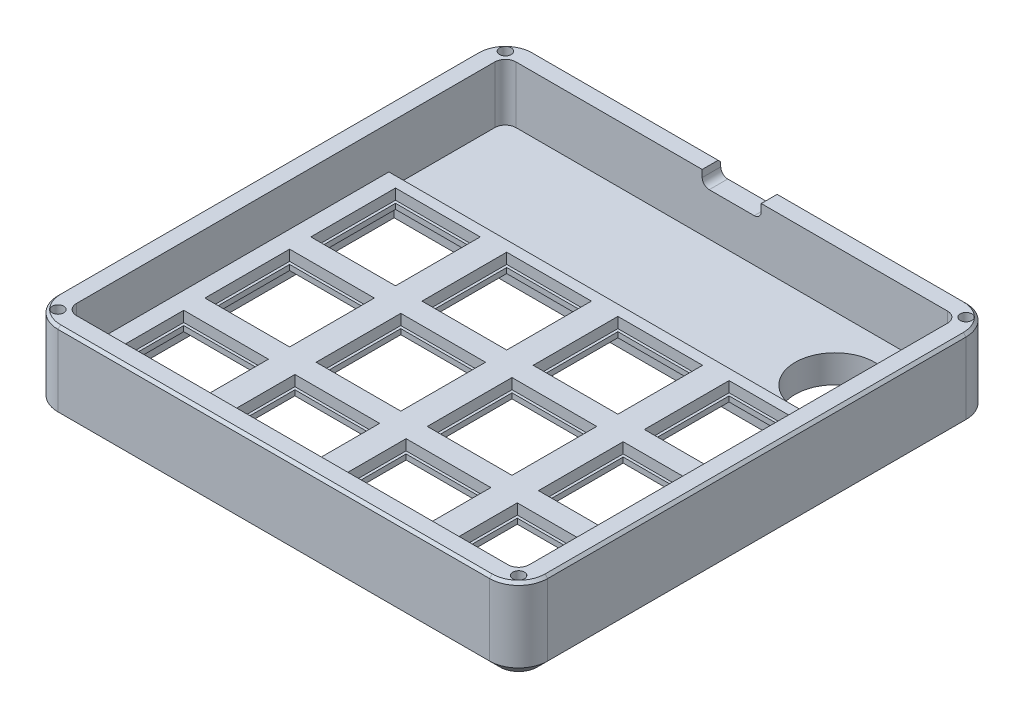
SolidWorks part; units mm, degrees
ref_plane "Front Plane" through (0, 0, 0) normal (0, 0, 1) x (1, 0, 0)
ref_plane "Top Plane" through (0, 0, 0) normal (0, 1, 0) x (1, 0, 0)
ref_plane "Right Plane" through (0, 0, 0) normal (1, 0, 0) x (0, 0, -1)
sketch "Sketch1" plane through (0, 0, 0) normal (0, 1, 0) x (1, 0, 0)
  line L0 (-42.7507, 39.5) -> (-42.7507, -39.5)
  line L1 (-40.75, -41.5007) -> (40.75, -41.5007)
  line L2 (42.7507, -39.5) -> (42.7507, 39.5)
  line L3 (40.75, 41.5007) -> (-40.75, 41.5007)
  line L4 (-42.7507, 0) -> (42.7507, 0) construction
  line L5 (0, 41.5007) -> (0, -41.5007) construction
  line L6 (-46.2507, 39.5) -> (-46.2507, -39.5)
  line L7 (-40.75, -45.0007) -> (40.75, -45.0007)
  line L8 (46.2507, -39.5) -> (46.2507, 39.5)
  line L9 (40.75, 45.0007) -> (-40.75, 45.0007)
  arc A0 (-40.75, 41.5007) -> (-42.7507, 39.5) centre (-40.75, 39.5) ccw
  arc A1 (-42.7507, -39.5) -> (-40.75, -41.5007) centre (-40.75, -39.5) ccw
  arc A2 (40.75, -41.5007) -> (42.7507, -39.5) centre (40.75, -39.5) ccw
  arc A3 (42.7507, 39.5) -> (40.75, 41.5007) centre (40.75, 39.5) ccw
  arc A4 (-40.75, 45.0007) -> (-46.2507, 39.5) centre (-40.75, 39.5) ccw
  arc A5 (-46.2507, -39.5) -> (-40.75, -45.0007) centre (-40.75, -39.5) ccw
  arc A6 (40.75, -45.0007) -> (46.2507, -39.5) centre (40.75, -39.5) ccw
  arc A7 (46.2507, 39.5) -> (40.75, 45.0007) centre (40.75, 39.5) ccw
  point P16 (0, 0)
  point P21 (0, 0)
  dimension "D1" = 79
  dimension "D2" = 81.5
  dimension "D3" = 2.0007
  dimension "D4" = 3.5
extrude "Boss-Extrude1" add sketch "Sketch1" along normal blind 16 contours L7 A6 L8 A7 L9 A4 L6 A5
sketch "Sketch3" plane through (0, 16, 0) normal (0, 1, 0) x (1, 0, 0)
  line L0 (-42.7507, 39.5) -> (-42.7507, -39.5) construction
  line L2 (-42.7507, 39.5) -> (-42.7507, -39.5)
  line L4 (42.7507, 39.5) -> (42.7507, -39.5)
  line L5 (-40.75, -41.5007) -> (40.75, -41.5007)
  line L8 (-40.75, 41.5007) -> (40.75, 41.5007)
  arc A0 (-42.7507, -39.5) -> (-40.75, -41.5007) centre (-40.75, -39.5) ccw
  arc A1 (40.75, -41.5007) -> (42.7507, -39.5) centre (40.75, -39.5) ccw
  arc A2 (-42.7507, 39.5) -> (-40.75, 41.5007) centre (-40.75, 39.5) cw
  arc A3 (40.75, 41.5007) -> (42.7507, 39.5) centre (40.75, 39.5) cw
extrude "Cut-Extrude1" cut sketch "Sketch3" against normal blind 8 contours L5 A1 L4 A3 L8 A2 L2 A0
sketch "Sketch4" plane through (0, 8, 0) normal (0, 1, 0) x (1, 0, 0)
  line L0 (-18.5007, 17.4993) -> (-18.5007, 1.4993)
  line L1 (-39.5007, 17.4993) -> (-23.5007, 17.4993)
  line L2 (-39.5007, 17.4993) -> (-39.5007, 1.4993)
  line L3 (-39.5007, 1.4993) -> (-23.5007, 1.4993)
  line L4 (-23.5007, 17.4993) -> (-23.5007, 1.4993)
  line L5 (-18.5007, 17.4993) -> (-2.5007, 17.4993)
  line L6 (-2.5007, 17.4993) -> (-2.5007, 1.4993)
  line L7 (-18.5007, 1.4993) -> (-2.5007, 1.4993)
  line L8 (2.4993, 17.4993) -> (2.4993, 1.4993)
  line L9 (2.4993, 17.4993) -> (18.4993, 17.4993)
  line L10 (18.4993, 17.4993) -> (18.4993, 1.4993)
  line L11 (2.4993, 1.4993) -> (18.4993, 1.4993)
  line L12 (23.4993, 17.4993) -> (23.4993, 1.4993)
  line L13 (23.4993, 17.4993) -> (39.4993, 17.4993)
  line L14 (39.4993, 17.4993) -> (39.4993, 1.4993)
  line L15 (23.4993, 1.4993) -> (39.4993, 1.4993)
  line L16 (-39.5007, -2.5007) -> (-39.5007, -18.5007)
  line L17 (-39.5007, -2.5007) -> (-23.5007, -2.5007)
  line L18 (-23.5007, -2.5007) -> (-23.5007, -18.5007)
  line L19 (-39.5007, -18.5007) -> (-23.5007, -18.5007)
  line L20 (-18.5007, -2.5007) -> (-18.5007, -18.5007)
  line L21 (-18.5007, -18.5007) -> (-2.5007, -18.5007)
  line L22 (-2.5007, -2.5007) -> (-2.5007, -18.5007)
  line L23 (-18.5007, -2.5007) -> (-2.5007, -2.5007)
  line L24 (2.4993, -2.5007) -> (2.4993, -18.5007)
  line L25 (2.4993, -18.5007) -> (18.4993, -18.5007)
  line L26 (18.4993, -2.5007) -> (18.4993, -18.5007)
  line L27 (2.4993, -2.5007) -> (18.4993, -2.5007)
  line L28 (23.4993, -2.5007) -> (23.4993, -18.5007)
  line L29 (23.4993, -18.5007) -> (39.4993, -18.5007)
  line L30 (39.4993, -2.5007) -> (39.4993, -18.5007)
  line L31 (23.4993, -2.5007) -> (39.4993, -2.5007)
  line L32 (-39.5007, -22.5007) -> (-39.5007, -38.5007)
  line L33 (-39.5007, -22.5007) -> (-23.5007, -22.5007)
  line L34 (-23.5007, -22.5007) -> (-23.5007, -38.5007)
  line L35 (-39.5007, -38.5007) -> (-23.5007, -38.5007)
  line L36 (-18.5007, -22.5007) -> (-18.5007, -38.5007)
  line L37 (-18.5007, -38.5007) -> (-2.5007, -38.5007)
  line L38 (-2.5007, -22.5007) -> (-2.5007, -38.5007)
  line L39 (-18.5007, -22.5007) -> (-2.5007, -22.5007)
  line L40 (2.4993, -22.5007) -> (2.4993, -38.5007)
  line L41 (2.4993, -38.5007) -> (18.4993, -38.5007)
  line L42 (18.4993, -22.5007) -> (18.4993, -38.5007)
  line L43 (2.4993, -22.5007) -> (18.4993, -22.5007)
  line L44 (23.4993, -22.5007) -> (23.4993, -38.5007)
  line L45 (23.4993, -38.5007) -> (39.4993, -38.5007)
  line L46 (39.4993, -22.5007) -> (39.4993, -38.5007)
  line L47 (23.4993, -22.5007) -> (39.4993, -22.5007)
  line L50 (-40.75, -41.5007) -> (40.75, -41.5007) construction
  point P19 (-18.5007, 9.4993)
  point P51 (-31.5, -30.5007)
  point P54 (-31.5007, 9.4993)
  point P57 (-23.5007, 9.4993)
  point P58 (-10.5, -30.5007)
  point P59 (-31.5007, 17.4993)
  point P60 (-10.5, -5.2481)
  point P61 (-10.5, 9.4993)
  point P62 (10.5, 9.4993)
  point P63 (10.5, -10.5007)
  point P64 (10.5, -30.5007)
  point P65 (-31.5, -10.5007)
  point P66 (31.5, -30.5007)
  point P67 (31.5, -10.5007)
  point P68 (31.5, 9.4993)
  dimension "D1" = 16
  dimension "D2" = 4
  dimension "D3" = 5
  dimension "D4" = 3
  dimension "D5" = 4
  dimension "D7" = 3
extrude "Cut-Extrude2" cut sketch "Sketch4" against normal through all
sketch "Sketch5" plane through (0, 16, 0) normal (0, 1, 0) x (1, 0, 0)
  line L2 (39.4993, 17.4993) -> (23.4993, 17.4993) construction
  line L7 (31.4993, 17.4993) -> (31.4993, 41.5007) construction
  line L8 (-40.75, 41.5007) -> (40.75, 41.5007) construction
  circle A0 centre (31.4993, 29.5) radius 7.5
  point P3 (31.4993, 17.4993)
  dimension "D1" = 15
extrude "Cut-Extrude3" cut sketch "Sketch5" against normal through all
sketch "Sketch7" plane through (0, 0, 0) normal (0, -1, 0) x (1, 0, 0)
  line L0 (42.7507, 39.5) -> (42.7507, -39.5) construction
  line L2 (-42.7507, 39.5) -> (-42.7507, -20.4993)
  line L3 (-42.7507, -20.4993) -> (42.7507, -20.4993)
  line L4 (42.7507, 39.5) -> (42.7507, -20.4993)
  line L5 (-40.75, 41.5007) -> (40.75, 41.5007)
  line L6 (-23.5007, -17.4993) -> (-39.5007, -17.4993) construction
  arc A0 (-42.7507, 39.5) -> (-40.75, 41.5007) centre (-40.75, 39.5) cw
  arc A1 (40.75, 41.5007) -> (42.7507, 39.5) centre (40.75, 39.5) cw
  dimension "D1" = 3
extrude "Cut-Extrude5" cut sketch "Sketch7" against normal blind 5
sketch "Sketch9" plane through (0, 16, 0) normal (0, 1, 0) x (1, 0, 0)
  line L0 (0, 45.0007) -> (0, -45.0007) construction
  line L1 (40.75, 45.0007) -> (-40.75, 45.0007) construction
  line L2 (-40.75, -45.0007) -> (40.75, -45.0007) construction
  line L3 (-46.2507, 0) -> (46.2507, 0) construction
  line L4 (-46.2507, 39.5) -> (-46.2507, -39.5) construction
  line L5 (46.2507, -39.5) -> (46.2507, 39.5) construction
  line L6 (-46.2507, 39.5) -> (-40.75, 45.0007) construction
  circle A0 centre (-43.5004, 42.2504) radius 1.1
  circle A1 centre (43.5004, 42.2504) radius 1.1
  circle A2 centre (43.5004, -42.2504) radius 1.1
  circle A3 centre (-43.5004, -42.2504) radius 1.1
  point P23 (-43.5004, 42.2504)
  dimension "D1" = 2.2
extrude "Cut-Extrude7" cut sketch "Sketch9" against normal blind 3
sketch "Sketch6" plane through (0, 8, 0) normal (0, -1, 0) x (1, 0, 0)
  line L0 (-42.7507, -39.5) -> (-42.7507, 39.5) construction
  line L1 (-42.7507, -20.4993) -> (42.7507, -20.4993)
  line L2 (-42.7507, -20.4993) -> (-42.7507, -39.5)
  line L4 (42.7507, -20.4993) -> (42.7507, -39.5)
  line L6 (-40.75, -41.5007) -> (40.75, -41.5007)
  line L7 (-42.7507, -20.4993) -> (42.7507, -20.4993) construction
  arc A0 (-42.7507, -39.5) -> (-40.75, -41.5007) centre (-40.75, -39.5) ccw
  arc A1 (40.75, -41.5007) -> (42.7507, -39.5) centre (40.75, -39.5) ccw
extrude "Cut-Extrude6" cut sketch "Sketch6" along normal offset from surface (2.75 mm away) 0.25 up to face at (0, 5, 20.3053)
chamfer "Chamfer1" distance 1 angle 45 1 edges at (0, 8, -20.4993)
chamfer "Chamfer2" distance 2 angle 45 8 edges at (0, 0, 45.0007) (44.6396, 0, 43.3896) (-44.6396, 0, 43.3896) (46.2507, 0, 0) (-46.2507, 0, 0) (44.6396, 0, -43.3896) (-44.6396, 0, -43.3896) (0, 0, -45.0007)
chamfer "Chamfer3" distance 0.5 angle 45 8 edges at (0, 16, -45.0007) (-44.6396, 16, -43.3896) (44.6396, 16, -43.3896) (-46.2507, 16, 0) (46.2507, 16, 0) (-44.6396, 16, 43.3896) (44.6396, 16, 43.3896) (0, 16, 45.0007)
sketch "Sketch11" plane through (0, 0, -45.0007) normal (0, 0, -1) x (-1, 0, 0)
  line L0 (-4.25, 14.675) -> (4.25, 14.675) construction
  line L1 (-4.25, 16) -> (4.25, 16) construction
  line L2 (-4.25, 13.35) -> (4.25, 13.35) construction
  line L5 (-40.75, 16) -> (40.75, 16) construction
  line L6 (-4.25, 13.35) -> (4.25, 13.35)
  line L7 (-5.575, 14.675) -> (-5.575, 16)
  line L8 (-5.575, 16) -> (5.575, 16)
  line L9 (5.575, 16) -> (5.575, 14.675)
  arc A0 (-4.25, 16) -> (-4.25, 13.35) centre (-4.25, 14.675) ccw construction
  arc A1 (4.25, 13.35) -> (4.25, 16) centre (4.25, 14.675) ccw construction
  arc A2 (-4.25, 13.35) -> (-5.575, 14.675) centre (-4.25, 14.675) cw
  arc A3 (4.25, 13.35) -> (5.575, 14.675) centre (4.25, 14.675) ccw
  point P2 (0, 14.675)
  dimension "D1" = 8.5
  dimension "D2" = 2.65
extrude "Cut-Extrude8" cut sketch "Sketch11" against normal up to surface (3.5 mm away) up to face at (0, 10.625, -41.5007)
sketch "Sketch12" plane through (0, 5, 0) normal (0, -1, 0) x (1, 0, 0)
  line L0 (-18.5007, 38.5007) -> (-18.5007, 22.5007)
  line L1 (-39.5007, 38.5007) -> (-23.5007, 38.5007)
  line L2 (-39.5007, 38.5007) -> (-39.5007, 22.5007)
  line L3 (-39.5007, 22.5007) -> (-23.5007, 22.5007)
  line L4 (-23.5007, 38.5007) -> (-23.5007, 22.5007)
  line L5 (-18.5007, 38.5007) -> (-2.5007, 38.5007)
  line L6 (-2.5007, 38.5007) -> (-2.5007, 22.5007)
  line L7 (-18.5007, 22.5007) -> (-2.5007, 22.5007)
  line L8 (2.4993, 38.5007) -> (2.4993, 22.5007)
  line L9 (2.4993, 38.5007) -> (18.4993, 38.5007)
  line L10 (18.4993, 38.5007) -> (18.4993, 22.5007)
  line L11 (2.4993, 22.5007) -> (18.4993, 22.5007)
  line L12 (23.4993, 38.5007) -> (23.4993, 22.5007)
  line L13 (23.4993, 38.5007) -> (39.4993, 38.5007)
  line L14 (39.4993, 38.5007) -> (39.4993, 22.5007)
  line L15 (23.4993, 22.5007) -> (39.4993, 22.5007)
  line L16 (-39.5007, 18.5007) -> (-39.5007, 2.5007)
  line L17 (-39.5007, 18.5007) -> (-23.5007, 18.5007)
  line L18 (-23.5007, 18.5007) -> (-23.5007, 2.5007)
  line L19 (-39.5007, 2.5007) -> (-23.5007, 2.5007)
  line L20 (23.4993, 18.5007) -> (23.4993, 2.5007)
  line L21 (23.4993, 2.5007) -> (39.4993, 2.5007)
  line L22 (39.4993, 18.5007) -> (39.4993, 2.5007)
  line L23 (23.4993, 18.5007) -> (39.4993, 18.5007)
  line L24 (2.4993, 18.5007) -> (2.4993, 2.5007)
  line L25 (2.4993, 2.5007) -> (18.4993, 2.5007)
  line L26 (18.4993, 18.5007) -> (18.4993, 2.5007)
  line L27 (2.4993, 18.5007) -> (18.4993, 18.5007)
  line L28 (-18.5007, 18.5007) -> (-18.5007, 2.5007)
  line L29 (-18.5007, 2.5007) -> (-2.5007, 2.5007)
  line L30 (-2.5007, 18.5007) -> (-2.5007, 2.5007)
  line L31 (-18.5007, 18.5007) -> (-2.5007, 18.5007)
  line L32 (-39.5007, -1.4993) -> (-39.5007, -17.4993)
  line L33 (-39.5007, -1.4993) -> (-23.5007, -1.4993)
  line L34 (-23.5007, -1.4993) -> (-23.5007, -17.4993)
  line L35 (-39.5007, -17.4993) -> (-23.5007, -17.4993)
  line L36 (23.4993, -1.4993) -> (23.4993, -17.4993)
  line L37 (23.4993, -17.4993) -> (39.4993, -17.4993)
  line L38 (39.4993, -1.4993) -> (39.4993, -17.4993)
  line L39 (23.4993, -1.4993) -> (39.4993, -1.4993)
  line L40 (2.4993, -1.4993) -> (2.4993, -17.4993)
  line L41 (2.4993, -17.4993) -> (18.4993, -17.4993)
  line L42 (18.4993, -1.4993) -> (18.4993, -17.4993)
  line L43 (2.4993, -1.4993) -> (18.4993, -1.4993)
  line L44 (-18.5007, -1.4993) -> (-18.5007, -17.4993)
  line L45 (-18.5007, -17.4993) -> (-2.5007, -17.4993)
  line L46 (-2.5007, -1.4993) -> (-2.5007, -17.4993)
  line L47 (-18.5007, -1.4993) -> (-2.5007, -1.4993)
  line L48 (-39.0007, 38.0007) -> (-39.0007, 23.0007)
  line L53 (-39.0007, 23.0007) -> (-24.0007, 23.0007)
  line L54 (-24.0007, 38.0007) -> (-24.0007, 23.0007)
  line L55 (-39.0007, 38.0007) -> (-24.0007, 38.0007)
  line L100 (-18.5007, 38.5007) -> (-18.5007, 22.5007) construction
  line L101 (-39.0007, 18.0007) -> (-39.0007, 3.0007)
  line L102 (-39.0007, 3.0007) -> (-24.0007, 3.0007)
  line L103 (-24.0007, 18.0007) -> (-24.0007, 3.0007)
  line L104 (-39.0007, 18.0007) -> (-24.0007, 18.0007)
  line L105 (-18.0007, 18.0007) -> (-18.0007, 3.0007)
  line L106 (-18.0007, 3.0007) -> (-3.0007, 3.0007)
  line L107 (-3.0007, 18.0007) -> (-3.0007, 3.0007)
  line L108 (-18.0007, 18.0007) -> (-3.0007, 18.0007)
  line L109 (2.9993, 18.0007) -> (2.9993, 3.0007)
  line L110 (2.9993, 3.0007) -> (17.9993, 3.0007)
  line L111 (17.9993, 18.0007) -> (17.9993, 3.0007)
  line L112 (2.9993, 18.0007) -> (17.9993, 18.0007)
  line L113 (23.9993, 18.0007) -> (23.9993, 3.0007)
  line L114 (23.9993, 3.0007) -> (38.9993, 3.0007)
  line L115 (38.9993, 18.0007) -> (38.9993, 3.0007)
  line L116 (23.9993, 18.0007) -> (38.9993, 18.0007)
  line L117 (23.9993, -1.9993) -> (23.9993, -16.9993)
  line L118 (23.9993, -16.9993) -> (38.9993, -16.9993)
  line L119 (38.9993, -1.9993) -> (38.9993, -16.9993)
  line L120 (23.9993, -1.9993) -> (38.9993, -1.9993)
  line L121 (2.9993, -1.9993) -> (2.9993, -16.9993)
  line L122 (2.9993, -16.9993) -> (17.9993, -16.9993)
  line L123 (17.9993, -1.9993) -> (17.9993, -16.9993)
  line L124 (2.9993, -1.9993) -> (17.9993, -1.9993)
  line L125 (-18.0007, -1.9993) -> (-18.0007, -16.9993)
  line L126 (-18.0007, -16.9993) -> (-3.0007, -16.9993)
  line L127 (-3.0007, -1.9993) -> (-3.0007, -16.9993)
  line L128 (-18.0007, -1.9993) -> (-3.0007, -1.9993)
  line L129 (-39.0007, -1.9993) -> (-39.0007, -16.9993)
  line L130 (-39.0007, -16.9993) -> (-24.0007, -16.9993)
  line L131 (-24.0007, -1.9993) -> (-24.0007, -16.9993)
  line L132 (-39.0007, -1.9993) -> (-24.0007, -1.9993)
  line L133 (-18.0007, 38.0007) -> (-18.0007, 23.0007)
  line L134 (-18.0007, 23.0007) -> (-3.0007, 23.0007)
  line L135 (-3.0007, 38.0007) -> (-3.0007, 23.0007)
  line L136 (-18.0007, 38.0007) -> (-3.0007, 38.0007)
  line L137 (2.9993, 38.0007) -> (2.9993, 23.0007)
  line L138 (2.9993, 23.0007) -> (17.9993, 23.0007)
  line L139 (17.9993, 38.0007) -> (17.9993, 23.0007)
  line L140 (2.9993, 38.0007) -> (17.9993, 38.0007)
  line L141 (23.9993, 38.0007) -> (23.9993, 23.0007)
  line L142 (23.9993, 23.0007) -> (38.9993, 23.0007)
  line L143 (38.9993, 38.0007) -> (38.9993, 23.0007)
  line L144 (23.9993, 38.0007) -> (38.9993, 38.0007)
  dimension "D7" = 0.5
  dimension "D1" = 4
  dimension "D2" = 3
  dimension "D3" = 0.5
  dimension "D4" = 0.5
extrude "Boss-Extrude2" add sketch "Sketch12" against normal blind 1 separate body
